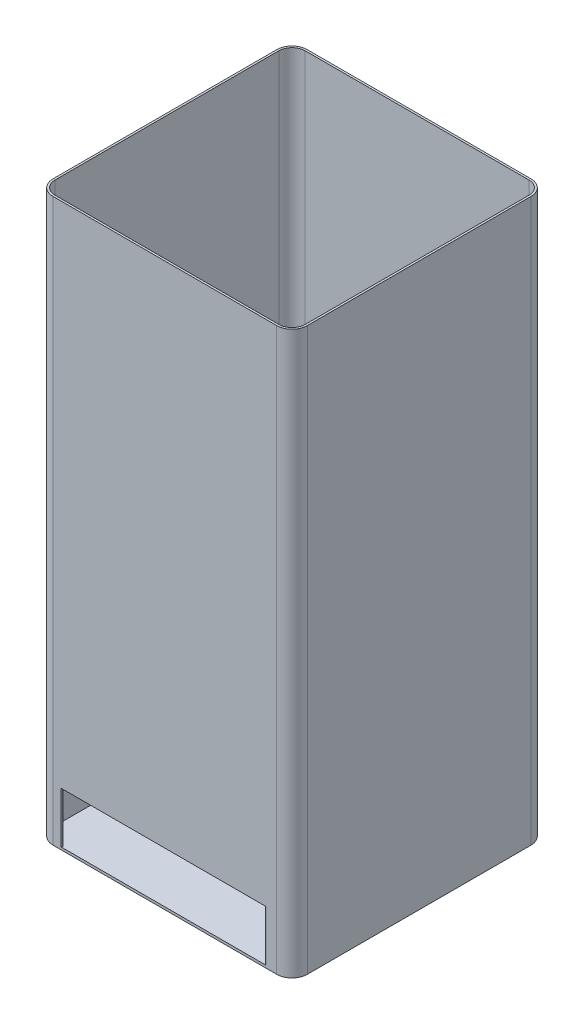
SolidWorks part; units mm, degrees
ref_plane "前视基准面" through (0, 0, 0) normal (0, 0, 1) x (1, 0, 0)
ref_plane "上视基准面" through (0, 0, 0) normal (0, 1, 0) x (1, 0, 0)
ref_plane "右视基准面" through (0, 0, 0) normal (1, 0, 0) x (0, 0, -1)
sketch "草图1" plane through (0, 0, 0) normal (0, 1, 0) x (1, 0, 0)
  line L1 (220, 250) -> (-220, 250)
  line L2 (250, 220) -> (250, -220)
  line L3 (220, -250) -> (-220, -250)
  line L4 (-250, 220) -> (-250, -220)
  line L5 (0, -250) -> (0, 250) construction
  line L6 (250, 0) -> (-250, 0) construction
  arc A0 (250, -220) -> (220, -250) centre (220, -220) cw
  arc A1 (-220, -250) -> (-250, -220) centre (-220, -220) cw
  arc A2 (220, 250) -> (250, 220) centre (220, 220) cw
  arc A3 (-220, 250) -> (-250, 220) centre (-220, 220) ccw
  point P0 (0, 0)
  point P8 (-250, -250)
  point P11 (250, 250)
  point P14 (-250, 250)
  dimension "D3" = 30
  dimension "D1" = 500
  dimension "D2" = 500
extrude "凸台-拉伸1" add sketch "草图1" along normal blind 5
sketch "草图2" plane through (0, 5, 0) normal (0, 1, 0) x (1, 0, 0)
  line L1 (-220, -250) -> (220, -250) construction
  line L2 (-220, -246) -> (-204.516, -246)
  line L3 (-246, 220) -> (-246, -220)
  line L4 (-220, 246) -> (220, 246)
  line L5 (246, 220) -> (246, -220)
  line L6 (250, -220) -> (250, 220)
  line L7 (220, 250) -> (-220, 250)
  line L8 (-250, 220) -> (-250, -220)
  line L9 (-220, -250) -> (220, -250)
  line L10 (250, -220) -> (250, 220)
  line L11 (220, 250) -> (-220, 250)
  line L12 (-250, 220) -> (-250, -220)
  line L13 (-220, -250) -> (-204.516, -250)
  line L14 (-203.016, -248.5) -> (-203.016, -247.5)
  line L15 (196.984, -248.5) -> (196.984, -247.5)
  line L16 (198.484, -246) -> (220, -246)
  line L17 (198.484, -250) -> (220, -250)
  arc A0 (-220, 246) -> (-246, 220) centre (-220, 220) ccw
  arc A1 (246, -220) -> (220, -246) centre (220, -220) cw
  arc A2 (220, 246) -> (246, 220) centre (220, 220) cw
  arc A3 (-246, -220) -> (-220, -246) centre (-220, -220) ccw
  arc A4 (220, -250) -> (250, -220) centre (220, -220) ccw
  arc A5 (250, 220) -> (220, 250) centre (220, 220) ccw
  arc A6 (-220, 250) -> (-250, 220) centre (-220, 220) ccw
  arc A7 (-250, -220) -> (-220, -250) centre (-220, -220) ccw
  arc A8 (220, -250) -> (250, -220) centre (220, -220) ccw
  arc A9 (250, 220) -> (220, 250) centre (220, 220) ccw
  arc A10 (-220, 250) -> (-250, 220) centre (-220, 220) ccw
  arc A11 (-250, -220) -> (-220, -250) centre (-220, -220) ccw
  arc A12 (198.484, -250) -> (196.984, -248.5) centre (198.484, -248.5) cw
  arc A13 (196.984, -247.5) -> (198.484, -246) centre (198.484, -247.5) cw
  arc A14 (-204.516, -250) -> (-203.016, -248.5) centre (-204.516, -248.5) ccw
  arc A15 (-203.016, -247.5) -> (-204.516, -246) centre (-204.516, -247.5) ccw
  point P5 (-3.016, -250)
  point P33 (196.984, -250)
  point P36 (196.984, -246)
  point P39 (-203.016, -250)
  dimension "D3" = 1.5
  dimension "D1" = 400
  dimension "D4" = 4
  dimension "D5" = 4
  dimension "D6" = 4
  dimension "D2" = 0
extrude "凸台-拉伸2" add sketch "草图2" along normal blind 100
sketch "草图3" plane through (0, 105, 0) normal (0, 1, 0) x (1, 0, 0)
  line L0 (-204.516, -246) -> (198.484, -246)
  line L8 (-204.516, -250) -> (198.484, -250)
  line L9 (196.984, -248.5) -> (196.984, -247.5)
  line L10 (198.484, -246) -> (220, -246)
  line L11 (246, -220) -> (246, 220)
  line L12 (220, 246) -> (-220, 246)
  line L13 (-246, 220) -> (-246, -220)
  line L14 (-220, -246) -> (-204.516, -246)
  line L15 (-203.016, -247.5) -> (-203.016, -248.5)
  line L16 (-204.516, -250) -> (198.484, -250)
  line L17 (196.984, -248.5) -> (196.984, -247.5)
  line L18 (198.484, -246) -> (220, -246)
  line L19 (246, -220) -> (246, 220)
  line L20 (220, 246) -> (-220, 246)
  line L21 (-246, 220) -> (-246, -220)
  line L22 (-220, -246) -> (-204.516, -246)
  line L23 (-203.016, -247.5) -> (-203.016, -248.5)
  line L28 (-246, -220) -> (-246, 220)
  line L29 (-220, 246) -> (220, 246)
  line L30 (246, 220) -> (246, -220)
  line L31 (220, -246) -> (198.484, -246)
  line L32 (196.984, -247.5) -> (196.984, -248.5)
  line L33 (198.484, -250) -> (220, -250)
  line L34 (250, -220) -> (250, 220)
  line L35 (220, 250) -> (-220, 250)
  line L36 (-250, 220) -> (-250, -220)
  line L37 (-220, -250) -> (-204.516, -250)
  line L38 (-203.016, -248.5) -> (-203.016, -247.5)
  line L39 (-204.516, -246) -> (-220, -246)
  line L40 (-246, -220) -> (-246, 220)
  line L41 (-220, 246) -> (220, 246)
  line L42 (246, 220) -> (246, -220)
  line L43 (220, -246) -> (198.484, -246)
  line L44 (196.984, -247.5) -> (196.984, -248.5)
  line L45 (198.484, -250) -> (220, -250)
  line L46 (250, -220) -> (250, 220)
  line L47 (220, 250) -> (-220, 250)
  line L48 (-250, 220) -> (-250, -220)
  line L49 (-220, -250) -> (-204.516, -250)
  line L50 (-203.016, -248.5) -> (-203.016, -247.5)
  line L51 (-204.516, -246) -> (-220, -246)
  arc A8 (-204.516, -250) -> (-203.016, -248.5) centre (-204.516, -248.5) ccw
  arc A9 (196.984, -248.5) -> (198.484, -250) centre (198.484, -248.5) ccw
  arc A10 (198.484, -246) -> (196.984, -247.5) centre (198.484, -247.5) ccw
  arc A11 (220, -246) -> (246, -220) centre (220, -220) ccw
  arc A12 (246, 220) -> (220, 246) centre (220, 220) ccw
  arc A13 (-220, 246) -> (-246, 220) centre (-220, 220) ccw
  arc A14 (-246, -220) -> (-220, -246) centre (-220, -220) ccw
  arc A15 (-203.016, -247.5) -> (-204.516, -246) centre (-204.516, -247.5) ccw
  arc A16 (-204.516, -250) -> (-203.016, -248.5) centre (-204.516, -248.5) ccw
  arc A17 (196.984, -248.5) -> (198.484, -250) centre (198.484, -248.5) ccw
  arc A18 (198.484, -246) -> (196.984, -247.5) centre (198.484, -247.5) ccw
  arc A19 (220, -246) -> (246, -220) centre (220, -220) ccw
  arc A20 (246, 220) -> (220, 246) centre (220, 220) ccw
  arc A21 (-220, 246) -> (-246, 220) centre (-220, 220) ccw
  arc A22 (-246, -220) -> (-220, -246) centre (-220, -220) ccw
  arc A23 (-203.016, -247.5) -> (-204.516, -246) centre (-204.516, -247.5) ccw
  arc A28 (-246, -220) -> (-220, -246) centre (-220, -220) ccw
  arc A29 (-220, 246) -> (-246, 220) centre (-220, 220) ccw
  arc A30 (246, 220) -> (220, 246) centre (220, 220) ccw
  arc A31 (220, -246) -> (246, -220) centre (220, -220) ccw
  arc A32 (198.484, -246) -> (196.984, -247.5) centre (198.484, -247.5) ccw
  arc A33 (196.984, -248.5) -> (198.484, -250) centre (198.484, -248.5) ccw
  arc A34 (220, -250) -> (250, -220) centre (220, -220) ccw
  arc A35 (250, 220) -> (220, 250) centre (220, 220) ccw
  arc A36 (-220, 250) -> (-250, 220) centre (-220, 220) ccw
  arc A37 (-250, -220) -> (-220, -250) centre (-220, -220) ccw
  arc A38 (-204.516, -250) -> (-203.016, -248.5) centre (-204.516, -248.5) ccw
  arc A39 (-203.016, -247.5) -> (-204.516, -246) centre (-204.516, -247.5) ccw
  arc A40 (-246, -220) -> (-220, -246) centre (-220, -220) ccw
  arc A41 (-220, 246) -> (-246, 220) centre (-220, 220) ccw
  arc A42 (246, 220) -> (220, 246) centre (220, 220) ccw
  arc A43 (220, -246) -> (246, -220) centre (220, -220) ccw
  arc A44 (198.484, -246) -> (196.984, -247.5) centre (198.484, -247.5) ccw
  arc A45 (196.984, -248.5) -> (198.484, -250) centre (198.484, -248.5) ccw
  arc A46 (220, -250) -> (250, -220) centre (220, -220) ccw
  arc A47 (250, 220) -> (220, 250) centre (220, 220) ccw
  arc A48 (-220, 250) -> (-250, 220) centre (-220, 220) ccw
  arc A49 (-250, -220) -> (-220, -250) centre (-220, -220) ccw
  arc A50 (-204.516, -250) -> (-203.016, -248.5) centre (-204.516, -248.5) ccw
  arc A51 (-203.016, -247.5) -> (-204.516, -246) centre (-204.516, -247.5) ccw
  arc M65 (-220, -246) -> (-246, -220) centre (-220, -220) cw
  line M66 (-246, -220) -> (-246, 220)
  arc M67 (-246, 220) -> (-220, 246) centre (-220, 220) cw
  line M68 (-220, 246) -> (220, 246)
  arc M69 (220, 246) -> (246, 220) centre (220, 220) cw
  line M70 (246, 220) -> (246, -220)
  arc M71 (246, -220) -> (220, -246) centre (220, -220) cw
  line M72 (220, -246) -> (198.484, -246)
  arc M73 (198.484, -246) -> (196.984, -247.5) centre (198.484, -247.5) ccw
  line M74 (196.984, -247.5) -> (196.984, -248.5)
  arc M75 (196.984, -248.5) -> (198.484, -250) centre (198.484, -248.5) ccw
  line M76 (198.484, -250) -> (220, -250)
  arc M77 (220, -250) -> (250, -220) centre (220, -220) ccw
  line M78 (250, -220) -> (250, 220)
  arc M79 (250, 220) -> (220, 250) centre (220, 220) ccw
  line M80 (220, 250) -> (-220, 250)
  arc M81 (-220, 250) -> (-250, 220) centre (-220, 220) ccw
  line M82 (-250, 220) -> (-250, -220)
  arc M83 (-250, -220) -> (-220, -250) centre (-220, -220) ccw
  line M84 (-220, -250) -> (-204.516, -250)
  arc M85 (-204.516, -250) -> (-203.016, -248.5) centre (-204.516, -248.5) ccw
  line M86 (-203.016, -248.5) -> (-203.016, -247.5)
  arc M87 (-203.016, -247.5) -> (-204.516, -246) centre (-204.516, -247.5) ccw
  line M88 (-204.516, -246) -> (-220, -246)
  dimension "D1" = 0
  dimension "D2" = 0
extrude "凸台-拉伸3" add sketch "草图3" along normal blind 1000 contours M88 M65 M66 M67 M68 M69 M70 M71 M72 M73 M74 M75 M76 M77 M78 M79 M80 M81 M82 M83 M84 M85 M86 M87 | L16 L0 M85 M75 M74 M73 M87 M86
